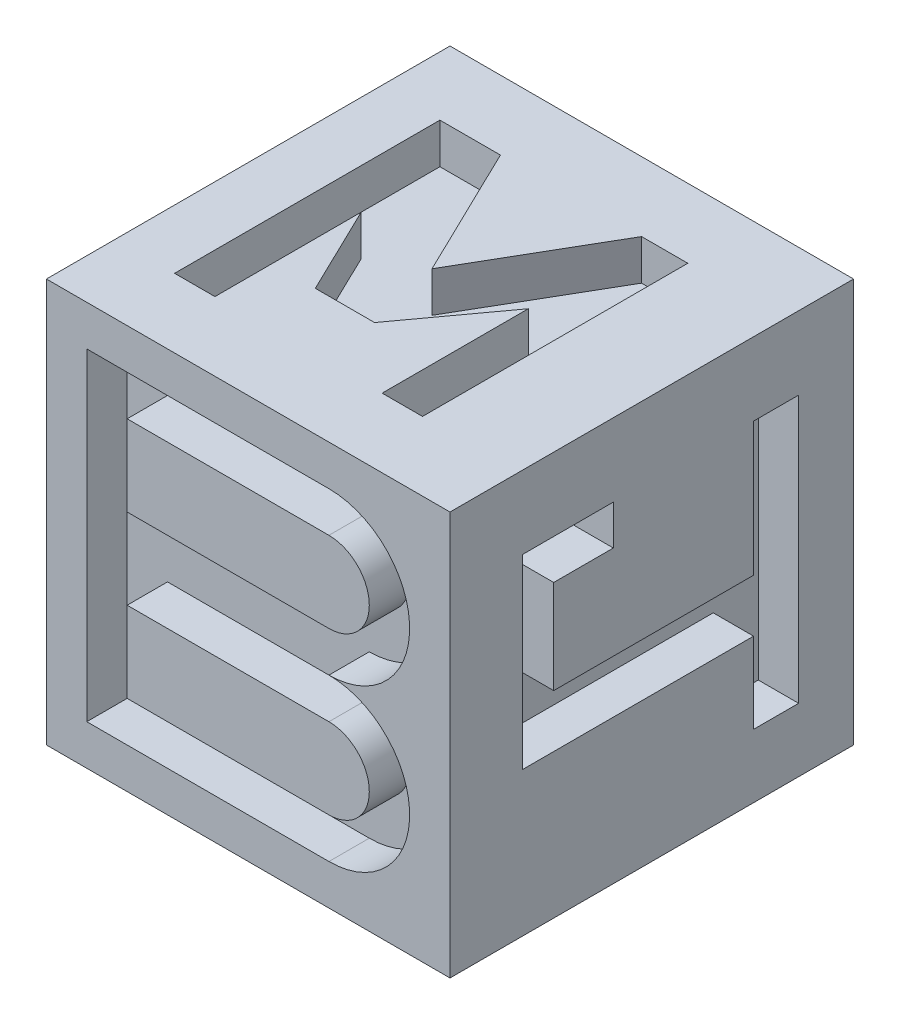
SolidWorks part; units mm, degrees
ref_plane "Front Plane" through (0, 0, 0) normal (0, 0, 1) x (1, 0, 0)
ref_plane "Top Plane" through (0, 0, 0) normal (0, 1, 0) x (1, 0, 0)
ref_plane "Right Plane" through (0, 0, 0) normal (1, 0, 0) x (0, 0, -1)
sketch "Sketch1" plane through (0, 0, 0) normal (0, 1, 0) x (1, 0, 0)
  line L1 (0, 0) -> (10, 0)
  line L2 (0, 0) -> (0, 10)
  line L3 (0, 10) -> (10, 10)
  line L4 (10, 0) -> (10, 10)
  dimension "D1" = 10
  dimension "D2" = 10
extrude "Boss-Extrude1" add sketch "Sketch1" along normal blind 10 contours L3 L4 L1 L2
sketch "Sketch2" plane through (0, 10, 0) normal (0, 1, 0) x (1, 0, 0)
  line L0 (1.4655, 1.7101) -> (1.4655, 8.2842)
  line L1 (1.4655, 8.2842) -> (2.9646, 8.2842)
  line L2 (2.9646, 8.2842) -> (4.5574, 4.9971)
  line L3 (4.5574, 4.9971) -> (6.4625, 8.2842)
  line L4 (6.4625, 8.2842) -> (7.6086, 8.2842)
  line L5 (7.6086, 8.2842) -> (7.6086, 1.7101)
  line L6 (7.6086, 1.7101) -> (6.6086, 1.7101)
  line L7 (6.6086, 1.7101) -> (6.6086, 5.3329)
  line L8 (6.6086, 5.3329) -> (5.0002, 3.1311)
  line L9 (5.0002, 3.1311) -> (3.5324, 3.1311)
  line L10 (3.5324, 3.1311) -> (2.4655, 5.3329)
  line L11 (2.4655, 5.3329) -> (2.4655, 1.7101)
  line L12 (2.4655, 1.7101) -> (1.4655, 1.7101)
  dimension "D1" = 1
  dimension "D2" = 1
extrude "Cut-Extrude1" cut sketch "Sketch2" against normal blind 1
sketch "Sketch3" plane through (10, 0, 0) normal (1, 0, 0) x (0, 0, -1)
  line L0 (8.6387, 8.1893) -> (8.6387, 1.5752)
  line L1 (8.6387, 1.5752) -> (7.5223, 1.5752)
  line L2 (7.5223, 1.5752) -> (7.5223, 3.5749)
  line L3 (7.5223, 3.5749) -> (1.7971, 3.5749)
  line L4 (1.7971, 3.5749) -> (1.7971, 8.1893)
  line L5 (1.7971, 8.1893) -> (4.0473, 8.1893)
  line L6 (4.0473, 8.1893) -> (4.0473, 7.2036)
  line L7 (4.0473, 7.2036) -> (2.5696, 7.2036)
  line L8 (2.5696, 7.2036) -> (2.5696, 4.8823)
  line L9 (2.5696, 4.8823) -> (7.5223, 4.8823)
  line L10 (7.5223, 4.8823) -> (7.5223, 8.1893)
  line L11 (7.5223, 8.1893) -> (8.6387, 8.1893)
extrude "Cut-Extrude2" cut sketch "Sketch3" against normal blind 1
sketch "Sketch4" plane through (0, 0, 0) normal (0, -1, 0) x (1, 0, 0)
  line L0 (7.1092, -8.1517) -> (2.6772, -8.1517)
  line L1 (2.6772, -8.1517) -> (2.6772, -7.1079)
  line L2 (2.6772, -7.1079) -> (4.2832, -7.1079)
  line L3 (4.2832, -7.1079) -> (4.2832, -3.0653)
  line L4 (4.2832, -3.0653) -> (2.4369, -3.0653)
  line L5 (2.4369, -3.0653) -> (2.4369, -1.9062)
  line L6 (2.4369, -1.9062) -> (8.875, -1.9062)
  line L7 (8.875, -1.9062) -> (8.875, -3.5536)
  line L8 (8.875, -3.5536) -> (6.4498, -3.5536)
  line L9 (6.4498, -3.5536) -> (6.4498, -7.1079)
  line L11 (6.4498, -7.1079) -> (7.1092, -7.1079)
  line L12 (7.1092, -7.1079) -> (7.1092, -8.1517)
extrude "Cut-Extrude3" cut sketch "Sketch4" against normal blind 1
sketch "Sketch5" plane through (0, 0, 0) normal (-1, 0, 0) x (0, 0, 1)
  line L0 (-1.6369, 2.1664) -> (-8.4378, 2.1664)
  line L1 (-8.4378, 2.1664) -> (-8.4378, 7.8483)
  line L2 (-8.4378, 7.8483) -> (-1.6369, 7.8483)
  line L3 (-1.6369, 7.8483) -> (-1.6369, 6.5372)
  line L4 (-1.6369, 6.5372) -> (-4.0038, 6.5372)
  line L5 (-4.0038, 6.5372) -> (-4.0038, 3.9291)
  line L6 (-4.0038, 3.9291) -> (-1.6369, 3.9291)
  line L7 (-1.6369, 3.9291) -> (-1.6369, 2.1664)
  line L8 (-7.2761, 3.9291) -> (-5.0373, 3.9291)
  line L9 (-5.0373, 3.9291) -> (-5.0373, 6.5372)
  line L10 (-5.0373, 6.5372) -> (-7.2761, 6.5372)
  line L11 (-7.2761, 6.5372) -> (-7.2761, 3.9291)
extrude "Cut-Extrude4" cut sketch "Sketch5" against normal blind 1
sketch "Sketch6" plane through (0, 0, -10) normal (0, 0, -1) x (-1, 0, 0)
  line L0 (-9, 9) -> (-1, 9)
  line L1 (-1, 9) -> (-1, 8)
  line L2 (-1, 8) -> (-4.5, 8)
  line L3 (-4.5, 8) -> (-4.5, 1)
  line L4 (-4.5, 1) -> (-5.5, 1)
  line L5 (-5.5, 1) -> (-5.5, 8)
  line L6 (-5.5, 8) -> (-9, 8)
  line L7 (-9, 8) -> (-9, 9)
  line L8 (-10, 10) -> (-10, 0) construction
  line L9 (0, 10) -> (-10, 10) construction
  line L10 (0, 0) -> (-10, 0) construction
  dimension "D1" = 1
  dimension "D2" = 1
  dimension "D3" = 8
  dimension "D4" = 1
  dimension "D5" = 3.5
  dimension "D6" = 1
  dimension "D7" = 1
extrude "Cut-Extrude5" cut sketch "Sketch6" against normal blind 1
sketch "Sketch7" plane through (0, 0, 0) normal (0, 0, 1) x (1, 0, 0)
  line L0 (1, 9) -> (1, 1)
  line L1 (1, 1) -> (7, 1)
  line L2 (1, 9) -> (7, 9)
  line L3 (0, 10) -> (0, 0) construction
  line L4 (0, 10) -> (10, 10) construction
  line L5 (0, 0) -> (10, 0) construction
  line L6 (9, 8.6962) -> (9, 1.3975) construction
  line L7 (10, 10) -> (10, 0) construction
  line L8 (2, 8) -> (2, 6)
  line L9 (2, 6) -> (7, 6)
  line L10 (2, 8) -> (7, 8)
  line L11 (7, 4) -> (2, 4)
  line L12 (2, 4) -> (2, 2)
  line L13 (2, 2) -> (7, 2)
  arc A0 (7, 9) -> (7, 5) centre (7, 7) cw
  arc A1 (7, 5) -> (7, 1) centre (7, 3) cw
  arc A2 (7, 8) -> (7, 6) centre (7, 7) cw
  arc A3 (7, 4) -> (7, 2) centre (7, 3) cw
  point P15 (1, 5)
  point P28 (0, 0)
  point P29 (0, 0)
  dimension "D1" = 1
  dimension "D2" = 1
  dimension "D3" = 1
  dimension "D4" = 1
  dimension "D5" = 1
  dimension "D6" = 1
  dimension "D7" = 1
  dimension "D8" = 1
extrude "Cut-Extrude6" cut sketch "Sketch7" against normal blind 1 contours A1 A0 L2 L0 L1 L10 A2 L9 L8 L11 A3 L13 L12
